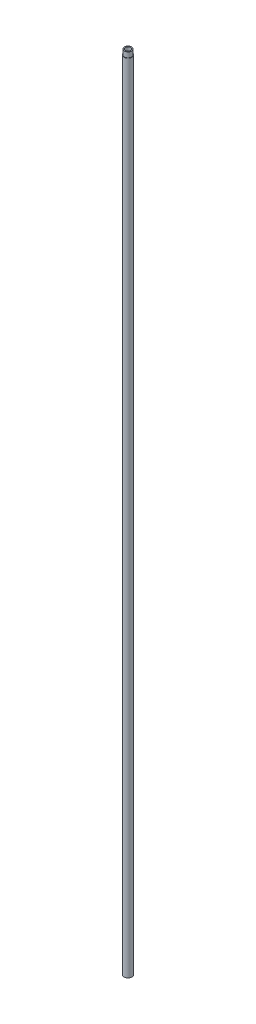
SolidWorks part; units mm, degrees
ref_plane "Alzado" through (0, 0, 0) normal (0, 0, 1) x (1, 0, 0)
ref_plane "Planta" through (0, 0, 0) normal (0, 1, 0) x (1, 0, 0)
ref_plane "Vista lateral" through (0, 0, 0) normal (1, 0, 0) x (0, 0, -1)
sketch "Croquis1" plane through (0, 0, 0) normal (0, 0, 1) x (1, 0, 0)
  line L0 (0, 37.2593) -> (0, -30.5297) construction
  line L1 (3.16, 34.1407) -> (4.26, 34.1407)
  line L2 (4.26, 34.1407) -> (4.26, 28.1407)
  line L3 (4.26, 28.1407) -> (4.76, 28.1407)
  line L4 (4.76, 28.1407) -> (4.76, -905.8593)
  line L5 (4.76, -905.8593) -> (3.76, -905.8593)
  line L6 (3.76, -905.8593) -> (3.76, -897.8593)
  line L7 (3.76, -897.8593) -> (3.16, -897.8593)
  line L8 (3.16, -897.8593) -> (3.16, 34.1407)
  dimension "D1" = 4.76
  dimension "D2" = 0.5
  dimension "D3" = 6
  dimension "D4" = 1.6
  dimension "D5" = 1
  dimension "D6" = 8
  dimension "D7" = 940
revolve "Revolución1" add sketch "Croquis1" angle 360 about L0
